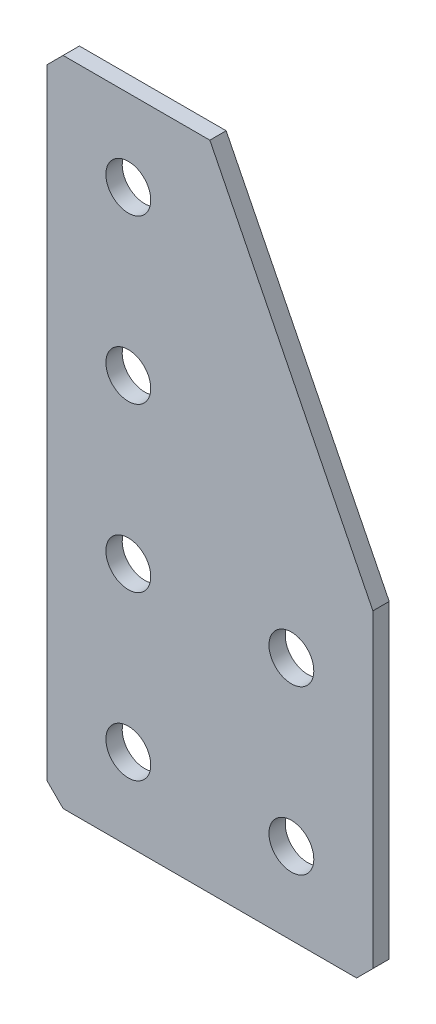
SolidWorks part; units mm, degrees
material "Простая углеродистая сталь"
ref_plane "Спереди(Плоскость XY)" through (0, 0, 0) normal (0, 0, 1) x (1, 0, 0)
ref_plane "Сверху(Плоскость XZ)" through (0, 0, 0) normal (0, 1, 0) x (1, 0, 0)
ref_plane "Справа(Плоскость ZY)" through (0, 0, 0) normal (1, 0, 0) x (0, 0, -1)
sketch "Эскиз1" plane through (0, 0, 0) normal (0, 0, -1) x (1, 0, 0)
  line L0 (0, 0) -> (0, 80)
  line L1 (0, 80) -> (40, 80)
  line L2 (40, 80) -> (40, 40)
  line L3 (40, 40) -> (20, 40) construction
  line L4 (20, 40) -> (20, 0) construction
  line L5 (20, 0) -> (0, 0)
  line L6 (40, 40) -> (20, 0)
  dimension "D1" = 80
  dimension "D2" = 40
  dimension "D3" = 20
  dimension "D4" = 20
extrude "Бобышка-Вытянуть1" add sketch "Эскиз1" along normal blind 2
hole_wizard "Отверстие с зазором M51" positions "Эскиз2" profile "Эскиз3" hole size "M5" standard "DIN" end condition through all
sketch "Эскиз2" plane through (0, 0, -2) normal (0, 0, -1) x (1, 0, 0)
  line L0 (10, 0) -> (10, 80) construction
  line L1 (0, 0) -> (20, 0) construction
  line L2 (40, 80) -> (0, 80) construction
  point P0 (10, 70)
  point P2 (10, 50)
  point P4 (10, 30)
  point P6 (10, 10)
  point P27 (30, 70)
  point P29 (30, 50)
  dimension "D1" = 20
  dimension "D2" = 20
  dimension "D3" = 20
  dimension "D4" = 10
  dimension "D5" = 20
sketch "Эскиз3" plane through (10, -70, -2) normal (1, 0, 0) x (0, 1, 0)
  line L0 (0, 0) -> (0, 2)
  line L1 (0, 2) -> (2.75, 2)
  line L2 (2.75, 2) -> (2.75, 0)
  line L5 (2.75, 0) -> (0, 0)
  line L11 (0, -6.35) -> (0, 107.95) construction
  dimension "Диаметр сквозного отверстия" = 5.5
  dimension "Глубина сквозного отверстия" = 2
chamfer "Фаска1" distance 2 angle 45 3 edges at (0, 0, -1) (40, -80, -1) (0, -80, -1)
